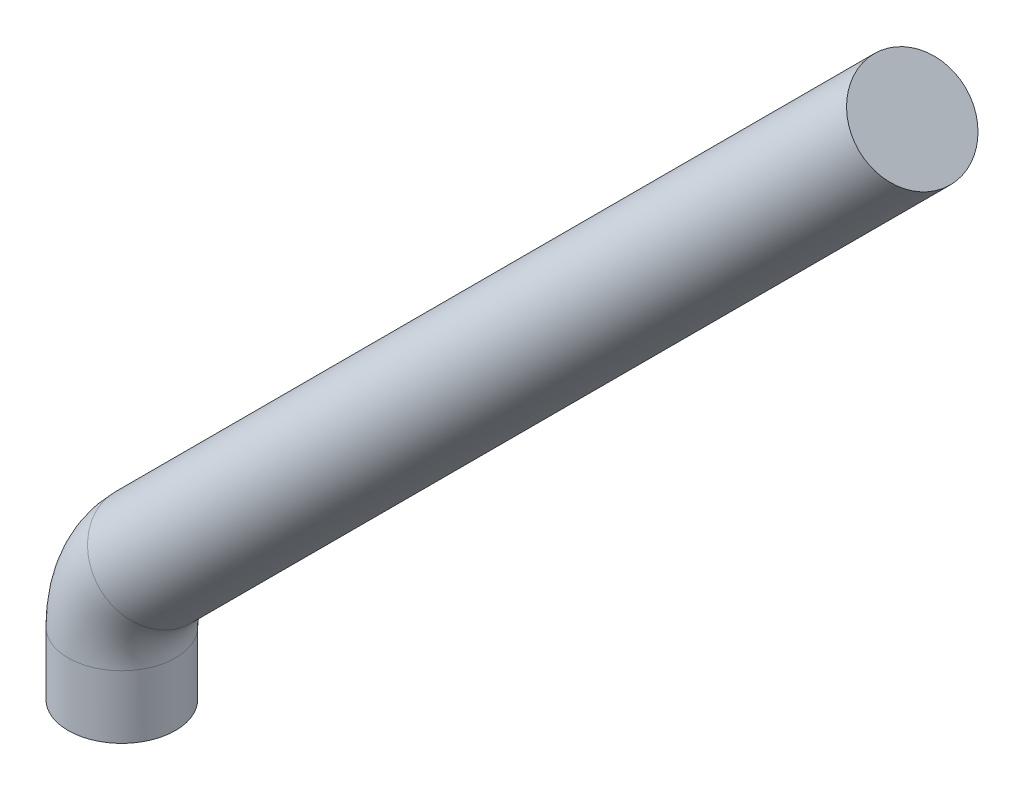
SolidWorks part; units mm, degrees
ref_plane "Front Plane" through (0, 0, 0) normal (0, 0, 1) x (1, 0, 0)
ref_plane "Top Plane" through (0, 0, 0) normal (0, 1, 0) x (1, 0, 0)
ref_plane "Right Plane" through (0, 0, 0) normal (1, 0, 0) x (0, 0, -1)
sketch "Sketch2" plane through (0, 0, 0) normal (0, 0, 1) x (1, 0, 0)
  line L0 (0, 0) -> (0, 0.1488)
  line L1 (0.0744, 0.3284) -> (1.8704, 2.1244)
  arc A0 (0.0744, 0.3284) -> (0, 0.1488) centre (0.254, 0.1488) ccw
  circle A1 centre (1.3816, -0.0593) radius 0.127
  point P6 (0, 0.254)
  dimension "D2" = 0.254
  dimension "D5" = 0.254
  dimension "D1" = 0.254
  dimension "D3" = 2.54
  dimension "D4" = 135
sweep "Sweep1" add path "Sketch2" circular profile diameter 0.254 parameters "D3"=0.254
